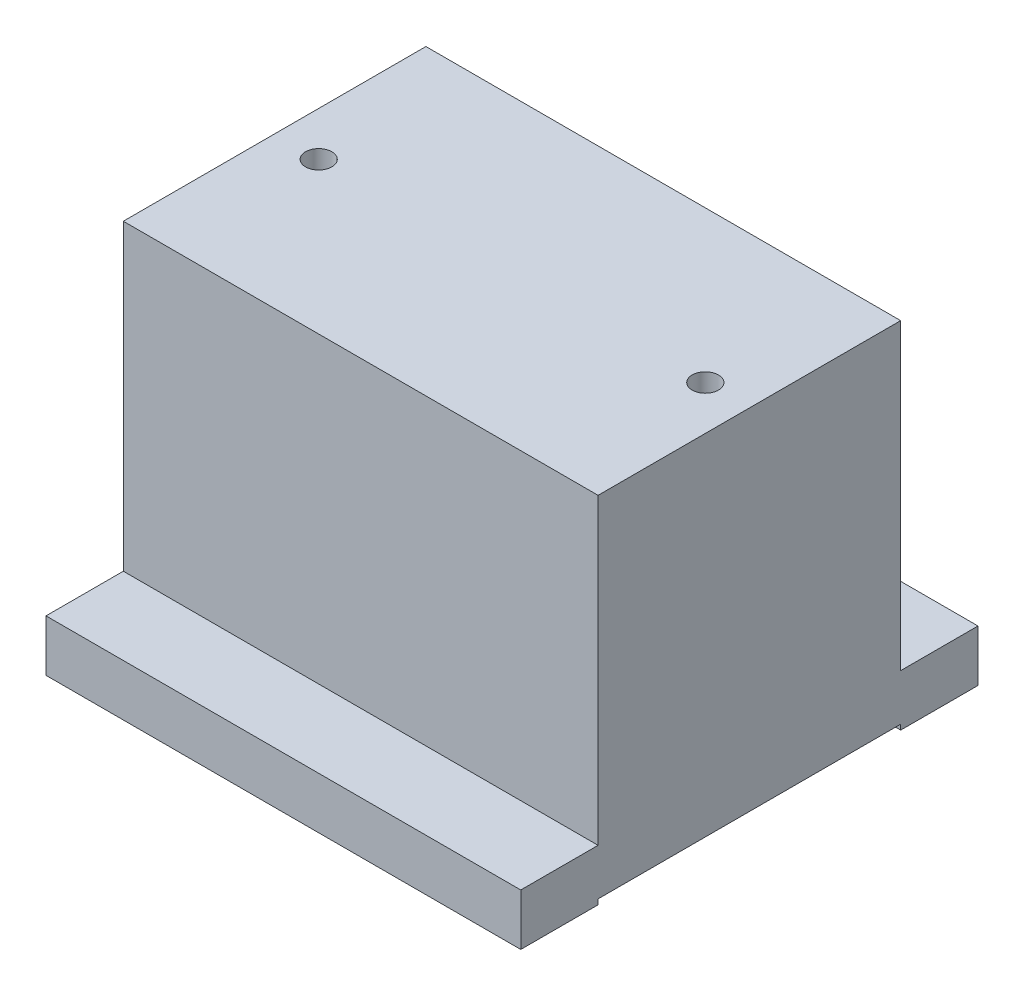
SolidWorks part; units mm, degrees
material "6061 Alloy"
ref_plane "Front" through (0, 0, 0) normal (0, 0, 1) x (1, 0, 0)
ref_plane "Top" through (0, 0, 0) normal (0, 1, 0) x (1, 0, 0)
ref_plane "Right" through (0, 0, 0) normal (1, 0, 0) x (0, 0, -1)
sketch "Sketch1" plane through (0, 0, 0) normal (0, 1, 0) x (1, 0, 0)
  line L1 (-46.05, 44.35) -> (46.05, 44.35)
  line L2 (-46.05, 44.35) -> (-46.05, -44.35)
  line L3 (-46.05, -44.35) -> (46.05, -44.35)
  line L4 (46.05, 44.35) -> (46.05, -44.35)
  line L5 (-46.05, 44.35) -> (46.05, -44.35) construction
  line L6 (-46.05, -44.35) -> (46.05, 44.35) construction
  point P0 (0, 0)
  dimension "D1" = 92.1
  dimension "D2" = 88.7
extrude "Boss-Extrude1" add sketch "Sketch1" along normal blind 10
sketch "Sketch2" plane through (0, 10, 0) normal (0, 1, 0) x (1, 0, 0)
  line L1 (-46.05, 29.35) -> (46.05, 29.35)
  line L2 (-46.05, 29.35) -> (-46.05, -29.35)
  line L3 (-46.05, -29.35) -> (46.05, -29.35)
  line L4 (46.05, 29.35) -> (46.05, -29.35)
  line L5 (-46.05, 29.35) -> (46.05, -29.35) construction
  line L6 (-46.05, -29.35) -> (46.05, 29.35) construction
  point P0 (0, 0)
  dimension "D1" = 58.7
  dimension "D2" = 92.1
extrude "Boss-Extrude2" add sketch "Sketch2" along normal blind 58.8
sketch "Sketch16" plane through (0, 0, 0) normal (0, -1, 0) x (1, 0, 0)
  line L0 (46.05, 44.35) -> (46.05, -44.35) construction
  line L1 (-46.05, 29.35) -> (46.05, 29.35)
  line L2 (-46.05, 29.35) -> (-46.05, -29.35)
  line L3 (-46.05, -29.35) -> (46.05, -29.35)
  line L4 (46.05, 29.35) -> (46.05, -29.35)
  line L5 (-46.05, 29.35) -> (46.05, -29.35) construction
  line L6 (-46.05, -29.35) -> (46.05, 29.35) construction
  line L7 (-46.05, 44.35) -> (46.05, 44.35) construction
  line L8 (46.05, -44.35) -> (-46.05, -44.35) construction
  point P0 (0, 0)
  dimension "D1" = 15
  dimension "D2" = 15
extrude "Cut-Extrude2" cut sketch "Sketch16" against normal blind 1
hole_wizard "1/4-20 Tapped Hole1" positions "Sketch27" profile "Sketch26" tap size "1/4-20" standard "Ansi Inch"
sketch "Sketch27" plane through (0, 68.8, 0) normal (0, 1, 0) x (-1, 0, 0)
  point P0 (37.5, 0)
  point P3 (-37.5, 0)
  dimension "D1" = 37.5
  dimension "D2" = 0
  dimension "D3" = 37.5
sketch "Sketch26" plane through (-37.5, 68.8, 0) normal (1, 0, 0) x (0, 0, 1)
  line L0 (0, 0) -> (0, 18.0438)
  line L1 (0, 18.0438) -> (2.5527, 16.51)
  line L2 (2.5527, 16.51) -> (2.5527, 0)
  line L5 (2.5527, 0) -> (0, 0)
  line L10 (0, 18.0438) -> (-2.5527, 16.51) construction
  line L11 (0, -6.35) -> (0, 107.95) construction
  dimension "Tap Drill Dia." = 5.1054
  dimension "Tap Drill Depth" = 16.51
  dimension "Drill Angle" = 118
